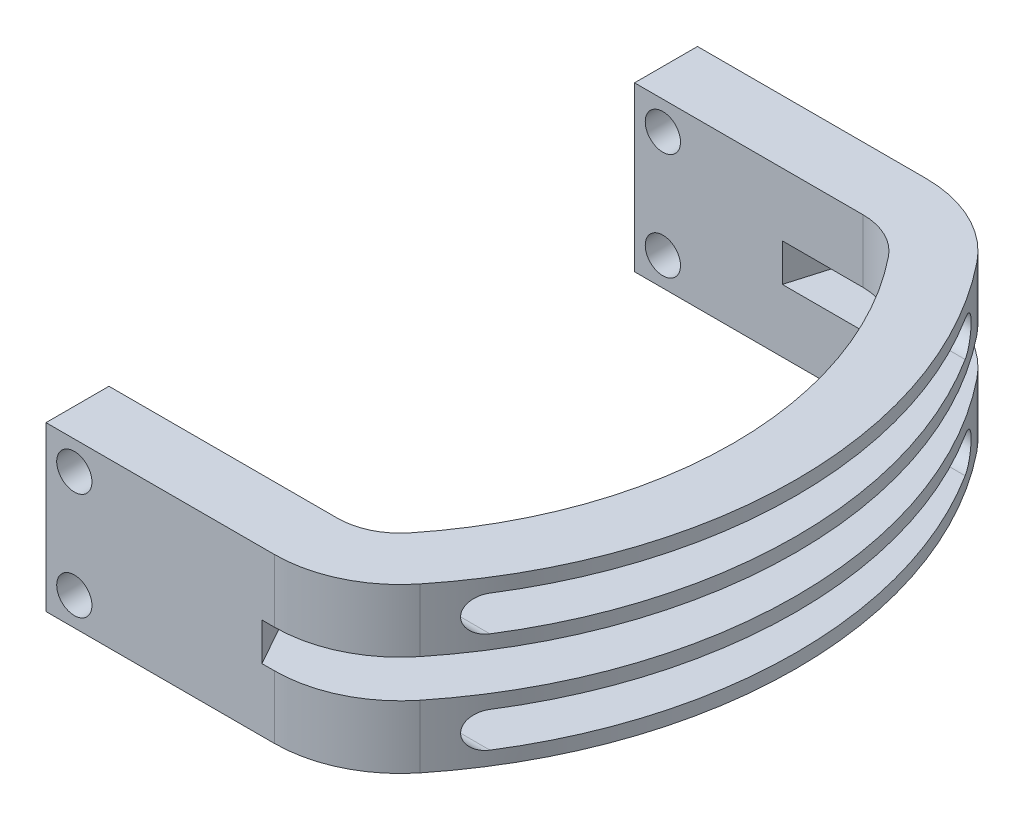
SolidWorks part; units mm, degrees
ref_plane "Plano frontal" through (0, 0, 0) normal (0, 0, 1) x (1, 0, 0)
ref_plane "Plano superior" through (0, 0, 0) normal (0, 1, 0) x (1, 0, 0)
ref_plane "Plano direito" through (0, 0, 0) normal (1, 0, 0) x (0, 0, -1)
sketch "Esboço1" plane through (0, 0, 0) normal (0, 1, 0) x (1, 0, 0)
  line L4 (0, 51.75) -> (18.1403, 51.75)
  line L5 (18.1403, 0) -> (0, 0)
  line L9 (0, 46.75) -> (18.1403, 46.75)
  line L10 (18.1403, 5) -> (0, 5)
  line L11 (0, 5) -> (0, 0)
  line L12 (0, 51.75) -> (0, 46.75)
  arc A1 (25.9429, 48.0046) -> (25.9429, 3.7454) centre (-1.6635, 25.875) cw
  arc A2 (25.9429, 3.7454) -> (18.1403, 0) centre (18.1403, 10) cw
  arc A3 (18.1403, 51.75) -> (25.9429, 48.0046) centre (18.1403, 41.75) cw
  arc A7 (18.1403, 46.75) -> (22.0416, 44.8773) centre (18.1403, 41.75) cw
  arc A8 (22.0416, 44.8773) -> (22.0416, 6.8727) centre (-1.6635, 25.875) cw
  arc A9 (22.0416, 6.8727) -> (18.1403, 5) centre (18.1403, 10) cw
  dimension "D2" = 10
  dimension "D1" = 35.3813
  dimension "D5" = 18.1403
  dimension "D3" = 5
  dimension "D4" = 41.75
extrude "Ressalto-extrusão1" add sketch "Esboço1" along normal mid plane 13
sketch "Esboço2" plane through (0, 0, 0) normal (-1, 0, 0) x (0, 0, 1)
  line L0 (-44.75, 4) -> (-7, 4) construction
  line L1 (-44.75, 2.6) -> (-7, 2.6)
  line L2 (-44.75, 5.4) -> (-7, 5.4)
  line L3 (18.5448, 0) -> (-18.5448, 0) construction
  line L5 (-46.75, 6.5) -> (-46.75, -6.5) construction
  line L6 (-5, 6.5) -> (-5, -6.5) construction
  line L7 (-44.75, -5.4) -> (-7, -5.4)
  line L8 (-44.75, -2.6) -> (-7, -2.6)
  line L9 (0, 0) -> (0, 1.5) construction
  line L10 (0, 6.5) -> (0, -6.5) construction
  line L11 (0, 1.5) -> (0, 6.5) construction
  arc A0 (-44.75, 2.6) -> (-44.75, 5.4) centre (-44.75, 4) cw
  arc A1 (-7, 2.6) -> (-7, 5.4) centre (-7, 4) ccw
  arc A2 (-44.75, -2.6) -> (-44.75, -5.4) centre (-44.75, -4) ccw
  arc A3 (-7, -2.6) -> (-7, -5.4) centre (-7, -4) cw
  point P25 (0, 4)
  dimension "D1" = 1.5
  dimension "D2" = 2
  dimension "D3" = 2
  dimension "D4" = 1.4
extrude "Corte-extrusão1" cut sketch "Esboço2" against normal through all
sketch "Esboço4" plane through (0, 6.5, 0) normal (0, 1, 0) x (1, 0, 0)
  line L0 (0, 0) -> (18.1403, 0) construction
  line L1 (18.1403, 51.75) -> (0, 51.75) construction
  line L2 (8.48, 35.63) -> (13.2033, 51.75)
  line L3 (11.37, 10.3) -> (17.1617, 0)
  line L4 (13.2033, 51.75) -> (33.7178, 51.75)
  line L5 (33.7178, 51.75) -> (33.7178, 0)
  line L6 (33.7178, 0) -> (17.1617, 0)
  arc A0 (11.37, 10.3) -> (8.48, 35.63) centre (39.995, 26.3958) cw
  arc A1 (25.9429, 3.7454) -> (25.9429, 48.0046) centre (-1.6635, 25.875) ccw construction
  dimension "D3" = 32.84
  dimension "D1" = 10.3
  dimension "D2" = 16.12
  dimension "D4" = 11.37
  dimension "D5" = 8.48
extrude "Corte-extrusão2" cut sketch "Esboço4" against normal mid plane 3 from surface at -6.5 starting at plane "Plano superior"
sketch "Esboço5" plane through (0, 0, -46.75) normal (0, 0, 1) x (1, 0, 0)
  line L0 (0, 6.5) -> (18.1403, 6.5) construction
  line L2 (18.5448, 0) -> (-18.5448, 0) construction
  line L3 (2.25, 4.25) -> (2.25, 6.5) construction
  line L4 (2.25, 4.25) -> (0, 4.25) construction
  line L5 (0, 6.5) -> (0, -6.5) construction
  circle A0 centre (2.25, 4.25) radius 1.4
  circle A1 centre (2.25, -4.25) radius 1.4
  dimension "D1" = 2.8
  dimension "D2" = 2.25
extrude "Corte-extrusão3" cut sketch "Esboço5" against normal through all both and the other way through all
